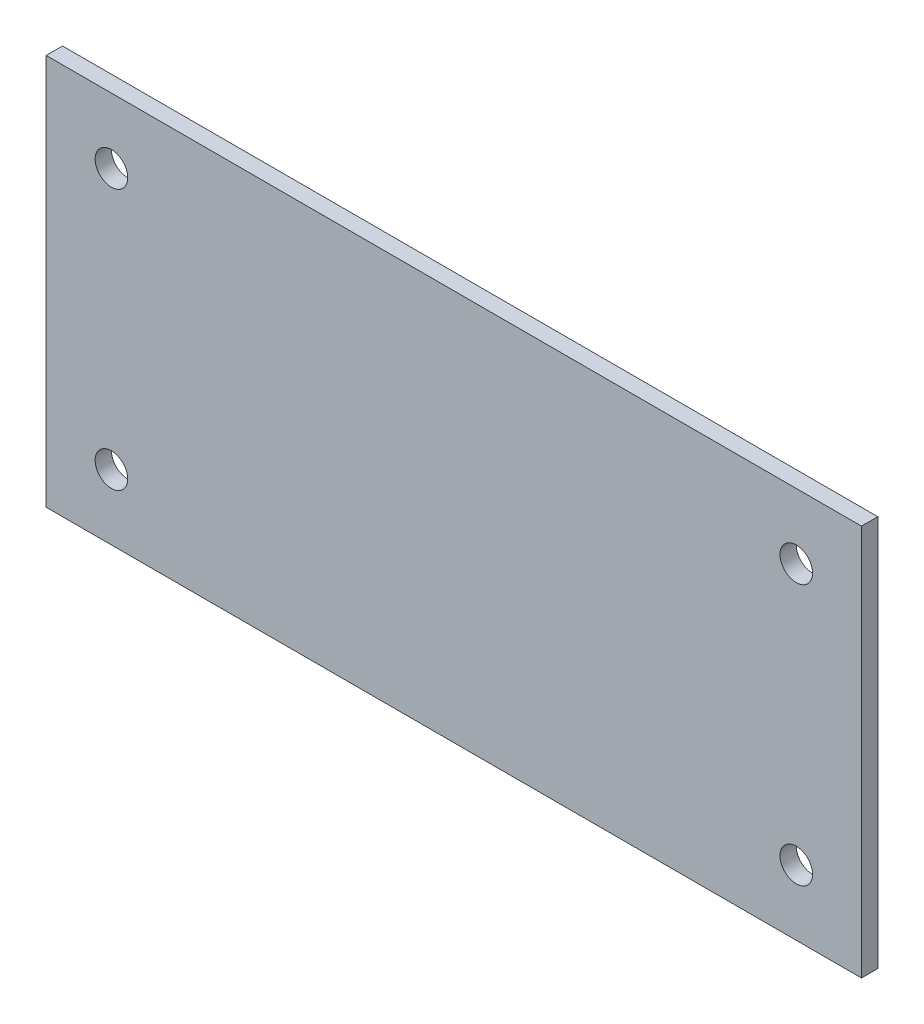
SolidWorks part; units mm, degrees
ref_plane "前视基准面" through (0, 0, 0) normal (0, 0, 1) x (1, 0, 0)
ref_plane "上视基准面" through (0, 0, 0) normal (0, 1, 0) x (1, 0, 0)
ref_plane "右视基准面" through (0, 0, 0) normal (1, 0, 0) x (0, 0, -1)
sketch "草图1" plane through (0, 0, 0) normal (0, 0, 1) x (1, 0, 0)
  line L0 (0, 0) -> (14.8416, 0) construction
  line L1 (-125, 60) -> (125, 60)
  line L2 (-125, 60) -> (-125, -60)
  line L3 (-125, -60) -> (125, -60)
  line L4 (125, 60) -> (125, -60)
  line L5 (0, 0) -> (0, 12.2563) construction
  circle A0 centre (-105, 40) radius 5
  circle A1 centre (105, 40) radius 5
  circle A2 centre (105, -40) radius 5
  circle A3 centre (-105, -40) radius 5
  dimension "D3" = 20
  dimension "D4" = 10
  dimension "D1" = 250
  dimension "D2" = 120
  dimension "1" = 20
extrude "凸台-拉伸1" add sketch "草图1" along normal blind 5
